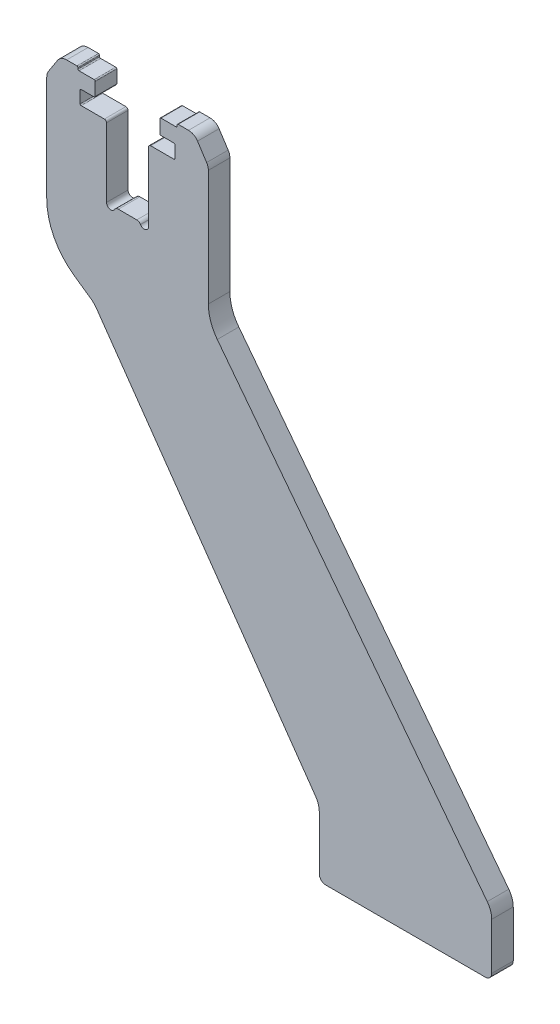
SolidWorks part; units mm, degrees
ref_plane "Plane1" through (0, 0, 0) normal (0, 0, 1) x (1, 0, 0)
ref_plane "Plane2" through (0, 0, 0) normal (0, 1, 0) x (1, 0, 0)
ref_plane "Plane3" through (0, 0, 0) normal (1, 0, 0) x (0, 0, -1)
sketch "Sketch1" plane through (0, 0, 0) normal (0, 0, 1) x (1, 0, 0)
  line L0 (-4.2859, 0) -> (4.2859, 0)
  line L1 (0, 0) -> (0, 32) construction
  line L2 (9.75, 0) -> (9.75, 32)
  line L3 (10.75, 33) -> (21.5, 33)
  line L4 (0, 0) -> (0, 42.7803) construction
  line L5 (-24.7073, -36.9575) -> (-16.9444, -42.3932)
  line L6 (41.6329, -29.3861) -> (166.9335, -192.6811)
  line L7 (169, -198.7687) -> (169, -220.5)
  line L8 (166, -223.5) -> (92, -223.5)
  line L9 (89, -220.5) -> (89, -195.799)
  line L10 (-14.4886, -44.849) -> (87.1915, -190.0633)
  line L12 (22, 33.5) -> (22, 39)
  line L13 (21.5, 39.5) -> (15.5, 39.5)
  line L14 (15, 40) -> (15, 46)
  line L15 (15.5, 46.5) -> (22.5, 46.5)
  line L16 (23, 47) -> (23, 47.5)
  line L18 (37.5, -17.2109) -> (37.5, 36.5178)
  line L19 (36.6922, 39.2427) -> (32.4788, 45.7249)
  line L20 (23.5, 48) -> (28.2866, 48)
  line L21 (-23.5, 48) -> (-28.2866, 48)
  line L22 (-36.6922, 39.2427) -> (-32.4788, 45.7249)
  line L23 (-37.5, -12.383) -> (-37.5, 36.5178)
  line L25 (-23, 47) -> (-23, 47.5)
  line L26 (-15.5, 46.5) -> (-22.5, 46.5)
  line L27 (-15, 40) -> (-15, 46)
  line L28 (-21.5, 39.5) -> (-15.5, 39.5)
  line L29 (-22, 33.5) -> (-22, 39)
  line L30 (-10.75, 33) -> (-21.5, 33)
  line L31 (-9.75, 0) -> (-9.75, 32)
  arc A0 (9.75, 0) -> (6.0179, -1) centre (7.75, 0) cw
  arc A1 (6.0179, -1) -> (4.2859, 0) centre (4.2859, -2) ccw
  arc A2 (-9.75, 0) -> (-6.0179, -1) centre (-7.75, 0) ccw
  arc A3 (-6.0179, -1) -> (-4.2859, 0) centre (-4.2859, -2) cw
  arc A4 (15.5, 39.5) -> (15, 40) centre (15.5, 40) cw
  arc A5 (22, 39) -> (21.5, 39.5) centre (21.5, 39) ccw
  arc A6 (21.5, 33) -> (22, 33.5) centre (21.5, 33.5) ccw
  arc A7 (-10.75, 33) -> (-9.75, 32) centre (-10.75, 32) cw
  arc A8 (-22, 33.5) -> (-21.5, 33) centre (-21.5, 33.5) ccw
  arc A9 (-21.5, 39.5) -> (-22, 39) centre (-21.5, 39) ccw
  arc A10 (-15, 40) -> (-15.5, 39.5) centre (-15.5, 40) cw
  arc A11 (9.75, 32) -> (10.75, 33) centre (10.75, 32) cw
  arc A12 (23, 47) -> (22.5, 46.5) centre (22.5, 47) cw
  arc A13 (15, 46) -> (15.5, 46.5) centre (15.5, 46) cw
  arc A14 (37.5, 36.5178) -> (36.6922, 39.2427) centre (32.5, 36.5178) ccw
  arc A15 (-36.6922, 39.2427) -> (-37.5, 36.5178) centre (-32.5, 36.5178) ccw
  arc A16 (-28.2866, 48) -> (-32.4788, 45.7249) centre (-28.2866, 43) ccw
  arc A17 (28.2866, 48) -> (32.4788, 45.7249) centre (28.2866, 43) cw
  arc A18 (23, 47.5) -> (23.5, 48) centre (23.5, 47.5) cw
  arc A19 (-15, 46) -> (-15.5, 46.5) centre (-15.5, 46) ccw
  arc A20 (-23, 47) -> (-22.5, 46.5) centre (-22.5, 47) ccw
  arc A21 (-23.5, 48) -> (-23, 47.5) centre (-23.5, 47.5) cw
  arc A22 (41.6329, -29.3861) -> (37.5, -17.2109) centre (57.5, -17.2109) cw
  arc A23 (-37.5, -12.383) -> (-24.7073, -36.9575) centre (-7.5, -12.383) ccw
  arc A24 (-16.9444, -42.3932) -> (-14.4886, -44.849) centre (-22.6802, -50.5847) cw
  arc A25 (166.9335, -192.6811) -> (169, -198.7687) centre (159, -198.7687) cw
  arc A26 (89, -195.799) -> (87.1915, -190.0633) centre (79, -195.799) ccw
  arc A27 (169, -220.5) -> (166, -223.5) centre (166, -220.5) cw
  arc A28 (92, -223.5) -> (89, -220.5) centre (92, -220.5) cw
  point P19 (37.5, -24)
  point P44 (15, 39.5)
  point P47 (22, 39.5)
  point P50 (22, 33)
  point P53 (-9.75, 33)
  point P56 (-22, 33)
  point P59 (-22, 39.5)
  point P62 (-15, 39.5)
  point P65 (9.75, 33)
  point P74 (37.5, 38)
  point P77 (-37.5, 38)
  point P80 (-31, 48)
  point P83 (31, 48)
  point P86 (23, 48)
  point P91 (169, -195.3741)
  point P95 (-23, 48)
  point P98 (-37.5, -28)
  point P101 (-15.5, -43.4046)
  point P105 (169, -223.5)
  dimension "D3" = 46
  dimension "D13" = 6.5
  dimension "D23" = 2
  dimension "D24" = 0.5
  dimension "D25" = 5
  dimension "D26" = 0.5
  dimension "D18" = 20
  dimension "D29" = 30
  dimension "D30" = 10
  dimension "D31" = 0.5
  dimension "D32" = 1
  dimension "D33" = 10
  dimension "D34" = 3
  dimension "D4" = 37.5
  dimension "D5" = 30
  dimension "D6" = 44
  dimension "D7" = 19.5
  dimension "D8" = 28.1259
  dimension "D9" = 72
  dimension "D10" = 8.5
  dimension "D11" = 7
  dimension "D12" = 206.5
  dimension "D14" = 271.5
  dimension "D15" = 48
  dimension "D16" = 80
  dimension "D17" = 75
  dimension "D19" = 10
  dimension "D20" = 8
  dimension "D21" = 35
  dimension "D22" = 76
  dimension "D27" = 55
  dimension "D28" = 22
extrude "Extrude1" add sketch "Sketch1" along normal blind 10
